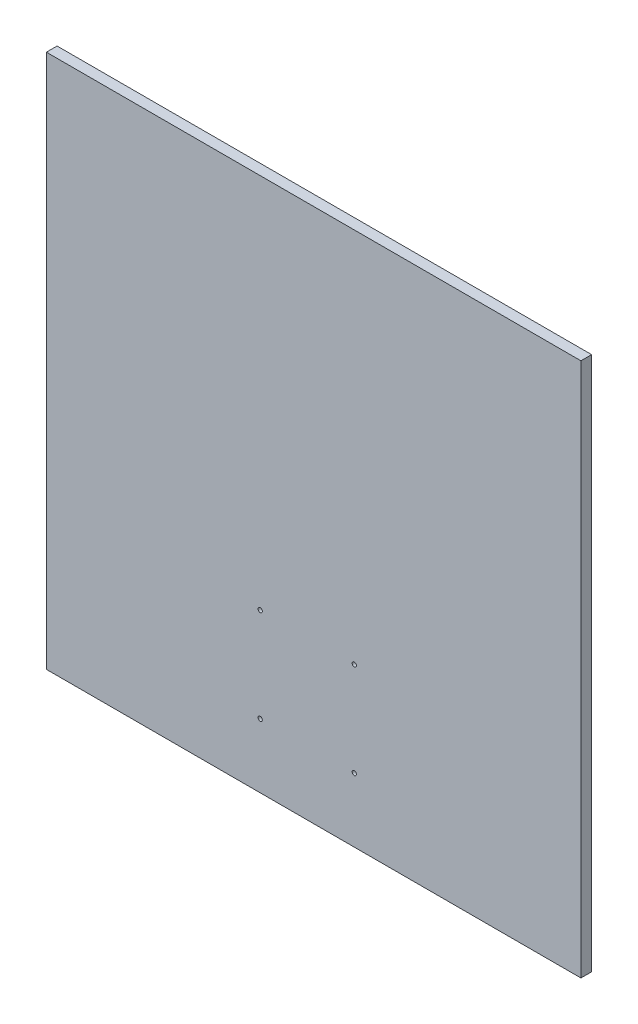
SolidWorks part; units mm, degrees
ref_plane "Plan de face" through (0, 0, 0) normal (0, 0, 1) x (1, 0, 0)
ref_plane "Plan de dessus" through (0, 0, 0) normal (0, 1, 0) x (1, 0, 0)
ref_plane "Plan de droite" through (0, 0, 0) normal (1, 0, 0) x (0, 0, -1)
sketch "Esquisse1" plane through (0, 0, 0) normal (0, 0, 1) x (1, 0, 0)
  line L1 (0, 0) -> (250, 0)
  line L2 (0, 0) -> (0, 250)
  line L3 (0, 250) -> (250, 250)
  line L4 (250, 0) -> (250, 250)
  circle A0 centre (100, 30) radius 1
  circle A1 centre (144, 30) radius 1
  circle A2 centre (144, 74) radius 1
  circle A3 centre (100, 74) radius 1
  dimension "D3" = 2
  dimension "D6" = 30
  dimension "D1" = 250
  dimension "D2" = 250
  dimension "D7" = 100
  dimension "D4" = 2
  dimension "D5" = 2
extrude "Boss.-Extru.1" add sketch "Esquisse1" along normal blind 5
